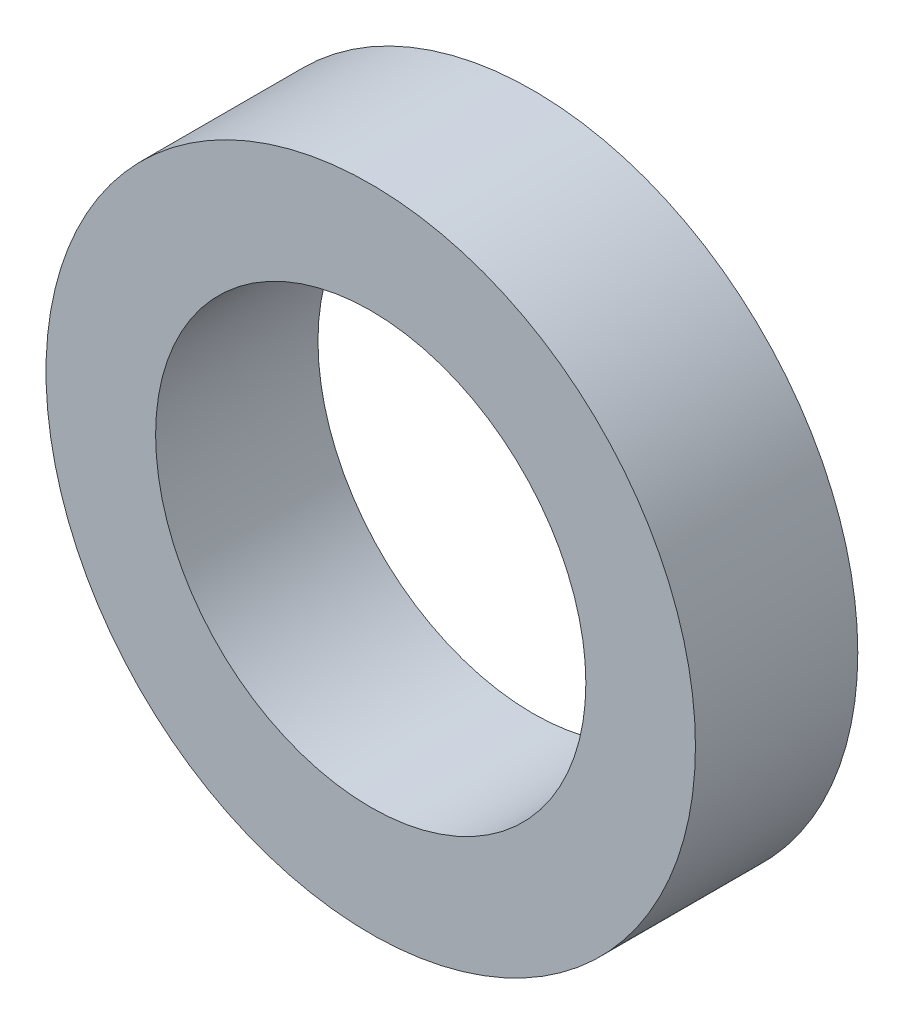
SolidWorks part; units mm, degrees
ref_plane "Front Plane" through (0, 0, 0) normal (0, 0, 1) x (1, 0, 0)
ref_plane "Top Plane" through (0, 0, 0) normal (0, 1, 0) x (1, 0, 0)
ref_plane "Right Plane" through (0, 0, 0) normal (1, 0, 0) x (0, 0, -1)
sketch "Sketch1" plane through (0, 0, 0) normal (0, 0, 1) x (1, 0, 0)
  line L0 (0, 2.65) -> (0, 4) construction
  line L1 (0, -2.65) -> (0, -4) construction
  circle A0 centre (0, 0) radius 4
  circle A1 centre (0, 0) radius 2.65
  dimension "OD" = 8
  dimension "ID" = 5.3
sketch "Sketch2" plane through (0, 0, 0) normal (1, 0, 0) x (0, 0, -1)
  line L0 (-1, 2.65) -> (1, 2.65) construction
  line L1 (-1, -2.65) -> (1, -2.65) construction
  line L2 (-1, -4) -> (1, -4) construction
  line L3 (-1, 4) -> (1, 4) construction
  dimension "Length" = 2
extrude "Extrude1" add sketch "Sketch1" along normal up to vertex (1 mm away) and the other way up to vertex (1 mm away) up to point (0, 2.65, 1) other way up to point (0, 2.65, -1)
sketch "Sketch3" plane through (0, 0, 1) normal (0, 0, 1) x (1, 0, 0)
  circle A0 centre (0, 0) radius 2.65 construction
  circle A3 centre (0, 0) radius 2.65
  point P3 (-2.65, 0)
